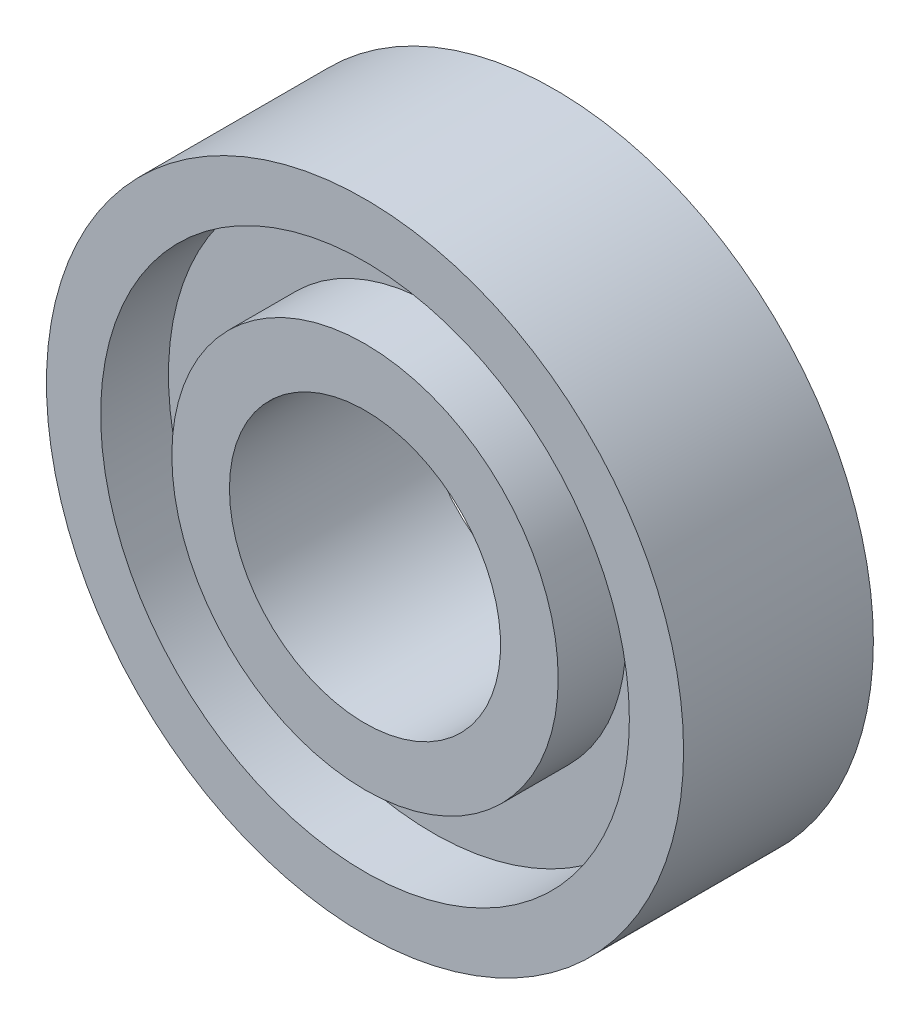
SolidWorks part; units mm, degrees
ref_plane "Front Plane" through (0, 0, 0) normal (0, 0, 1) x (1, 0, 0)
ref_plane "Top Plane" through (0, 0, 0) normal (0, 1, 0) x (1, 0, 0)
ref_plane "Right Plane" through (0, 0, 0) normal (1, 0, 0) x (0, 0, -1)
sketch "Sketch1" plane through (0, 0, 0) normal (0, 0, 1) x (1, 0, 0)
  circle A0 centre (0, 0) radius 23.5
  dimension "D1" = 47
extrude "Extrude1" add sketch "Sketch1" along normal blind 14
sketch "Sketch2" plane through (0, 0, 14) normal (0, 0, 1) x (1, 0, 0)
  circle A0 centre (0, 0) radius 14.25
  circle A1 centre (0, 0) radius 19.5
  dimension "D1" = 39
  dimension "D2" = 28.5
extrude "Extrude2" cut sketch "Sketch2" against normal blind 5
sketch "Sketch3" plane through (0, 0, 0) normal (0, 0, -1) x (-1, 0, 0)
  circle A0 centre (0, 0) radius 14.25
  circle A1 centre (0, 0) radius 19.5
  circle A2 centre (0, 0) radius 23.5 construction
  dimension "D1" = 39
  dimension "D2" = 28.5
  dimension "D3" = 0
extrude "Extrude3" cut sketch "Sketch3" against normal blind 5
sketch "Sketch4" plane through (0, 0, 0) normal (0, 0, -1) x (-1, 0, 0)
  circle A0 centre (0, 0) radius 10
  dimension "D1" = 20
extrude "Extrude4" cut sketch "Sketch4" against normal through all
